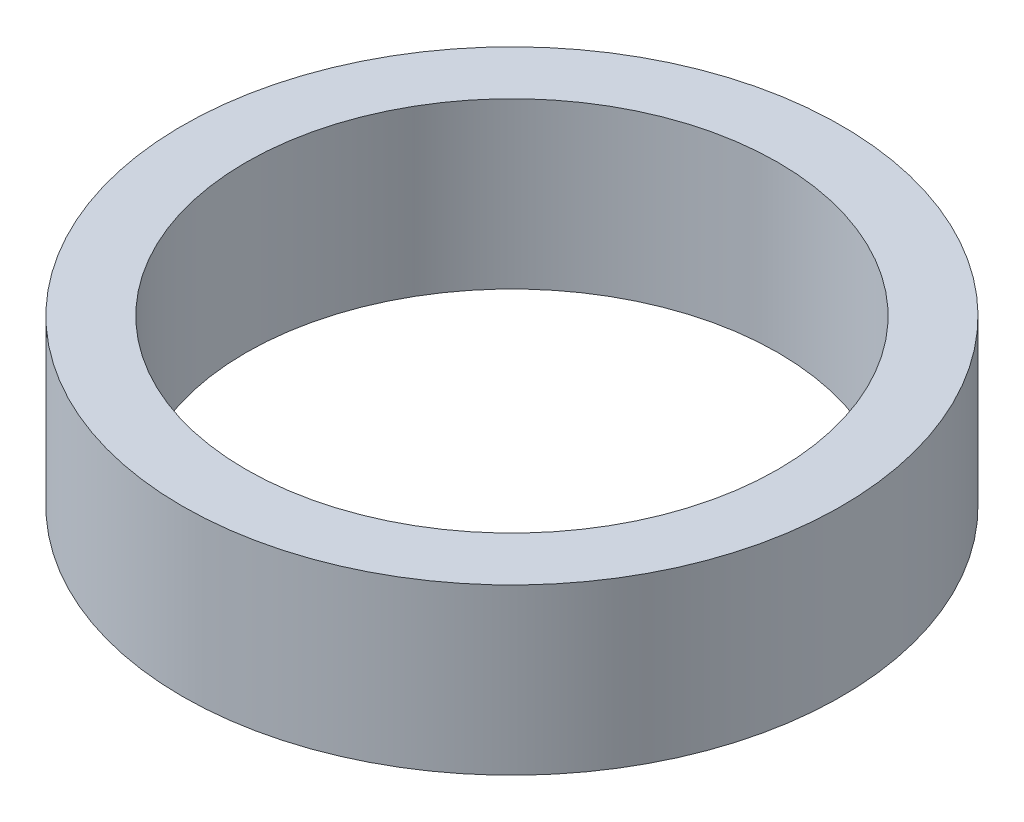
SolidWorks part; units mm, degrees
ref_plane "前视基准面" through (0, 0, 0) normal (0, 0, 1) x (1, 0, 0)
ref_plane "上视基准面" through (0, 0, 0) normal (0, 1, 0) x (1, 0, 0)
ref_plane "右视基准面" through (0, 0, 0) normal (1, 0, 0) x (0, 0, -1)
sketch "草图1" plane through (0, 0, 0) normal (0, 0, 1) x (1, 0, 0)
  line L0 (0, 161.3762) -> (0, 0) construction
  line L1 (141.7365, 0) -> (-131.7984, 0) construction
  line L2 (25.4, 0) -> (25.4, 12.7)
  line L3 (20.5, 12.7) -> (25.4, 12.7)
  line L4 (20.5, 0) -> (25.4, 0)
  line L7 (20.5, 12.7) -> (20.5, 0)
  dimension "D2" = 25.4
  dimension "D3" = 12.7
  dimension "D11" = 20.5
revolve "旋转1" add sketch "草图1" angle 360 about L0
cosmetic thread "装饰螺纹线1" parameters "D2"=42
